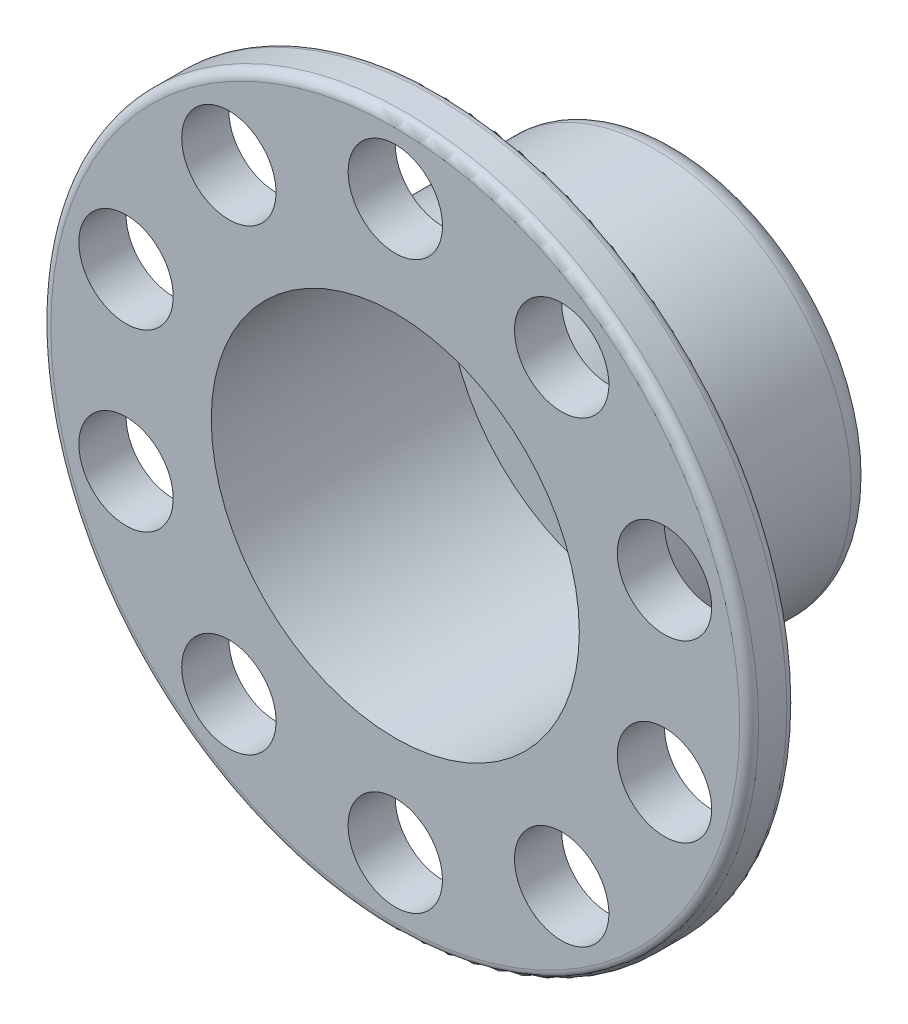
SolidWorks part; units mm, degrees
ref_plane "Front Plane" through (0, 0, 0) normal (0, 0, 1) x (1, 0, 0)
ref_plane "Top Plane" through (0, 0, 0) normal (0, 1, 0) x (1, 0, 0)
ref_plane "Right Plane" through (0, 0, 0) normal (1, 0, 0) x (0, 0, -1)
sketch "Sketch2" plane through (0, 0, 0) normal (0, 0, 1) x (1, 0, 0)
  circle A0 centre (0, 0) radius 75
  dimension "D1" = 150
extrude "Extrude-Thin1" add sketch "Sketch2" along normal blind 10 thin thin type one direction reverse wall 35
sketch "Sketch3" plane through (0, 0, 10) normal (0, 0, 1) x (1, 0, 0)
  circle A0 centre (0, 0) radius 39.005
  dimension "D1" = 78.01
extrude "Extrude-Thin2" add sketch "Sketch3" against normal blind 60 thin
sketch "Sketch4" plane through (0, 0, -50) normal (0, 0, -1) x (-1, 0, 0)
  circle A0 centre (0, 0) radius 39.005 construction
  circle A1 centre (0, 0) radius 39.005
extrude "Boss-Extrude1" add sketch "Sketch4" against normal blind 10
sketch "Sketch5" plane through (0, 0, 0) normal (0, 0, -1) x (-1, 0, 0)
  circle A0 centre (0, 0) radius 60 construction
  circle A1 centre (0, 60) radius 10
  circle A2 centre (35.2671, 48.541) radius 10
  circle A3 centre (57.0634, 18.541) radius 10
  circle A4 centre (57.0634, -18.541) radius 10
  circle A5 centre (35.2671, -48.541) radius 10
  circle A6 centre (0, -60) radius 10
  circle A7 centre (-35.2671, -48.541) radius 10
  circle A8 centre (-57.0634, -18.541) radius 10
  circle A9 centre (-57.0634, 18.541) radius 10
  circle A10 centre (-35.2671, 48.541) radius 10
  point P25 (0, 0)
  dimension "D1" = 120
  dimension "D2" = 20
  dimension "D3" = 10
extrude "Cut-Extrude1" cut sketch "Sketch5" against normal through all
fillet "Fillet1" radius 5 1 edges at (41.655, 0, -50)
fillet "Fillet2" radius 2 2 edges at (75, 0, 0) (75, 0, 10)
